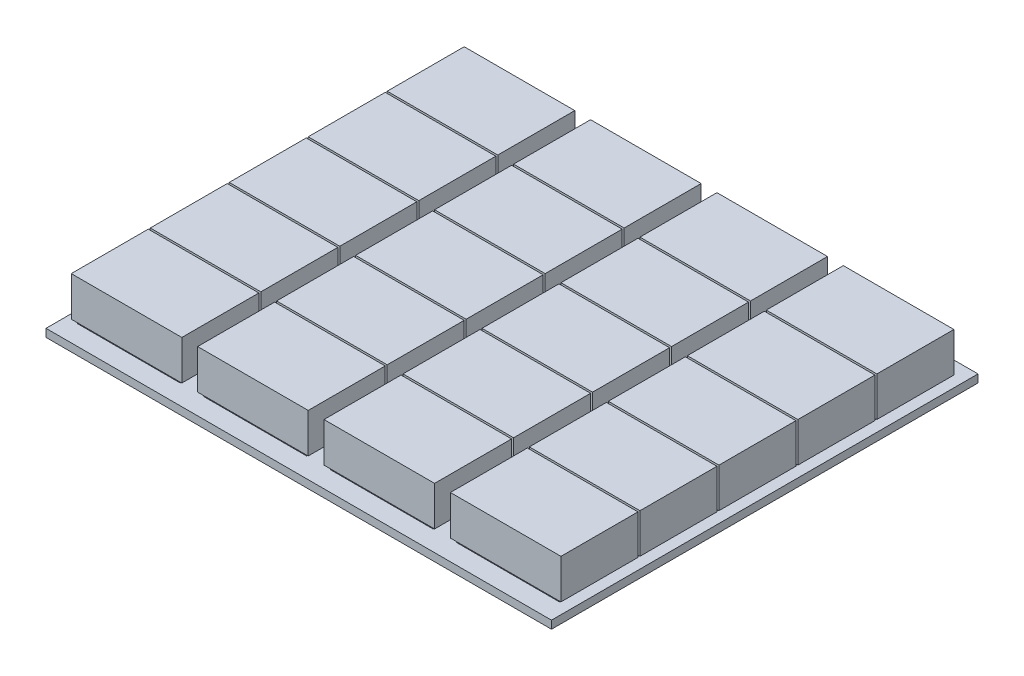
SolidWorks part; units mm, degrees
ref_plane "Front Plane" through (0, 0, 0) normal (0, 0, 1) x (1, 0, 0)
ref_plane "Top Plane" through (0, 0, 0) normal (0, 1, 0) x (1, 0, 0)
ref_plane "Right Plane" through (0, 0, 0) normal (1, 0, 0) x (0, 0, -1)
sketch "Sketch1" plane through (0, 0, 0) normal (0, 1, 0) x (1, 0, 0)
  line L1 (-40, -135) -> (40, -135)
  line L2 (-40, -135) -> (-40, 135)
  line L3 (-40, 135) -> (40, 135)
  line L4 (40, -135) -> (40, 135)
  line L5 (-40, -135) -> (40, 135) construction
  line L6 (-40, 135) -> (40, -135) construction
  point P0 (0, 0)
  dimension "D1" = 80
  dimension "D2" = 270
extrude "Boss-Extrude1" add sketch "Sketch1" along normal blind 5
sketch "Sketch2" plane through (0, 5, 0) normal (0, 1, 0) x (1, 0, 0)
  line L0 (0, 0) -> (0, -135) construction
  line L1 (-40, -135) -> (40, -135) construction
  line L3 (-32.5, -77.5) -> (32.5, -77.5)
  line L4 (-32.5, -77.5) -> (-32.5, -122.5)
  line L5 (-32.5, -122.5) -> (32.5, -122.5)
  line L6 (32.5, -77.5) -> (32.5, -122.5)
  line L7 (-32.5, -77.5) -> (32.5, -122.5) construction
  line L8 (-32.5, -122.5) -> (32.5, -77.5) construction
  point P5 (0, -100)
  dimension "D1" = 65
  dimension "D2" = 45
  dimension "D3" = 12.5
extrude "Boss-Extrude3" add sketch "Sketch2" along normal blind 2
pattern_linear "LPattern1" count 5 spacing 50 along (0, 0, -1) of "Boss-Extrude3"
sketch "Sketch3" plane through (0, 7, 0) normal (0, 1, 0) x (1, 0, 0)
  line L0 (0, 0) -> (0, -122.5) construction
  line L1 (-32.5, -122.5) -> (32.5, -122.5) construction
  line L2 (-40, 135) -> (-40, -135) construction
  line L3 (-35, -75.2605) -> (35, -75.2605)
  line L4 (-35, -75.2605) -> (-35, -124.0095)
  line L5 (-35, -124.0095) -> (35, -124.0095)
  line L6 (35, -75.2605) -> (35, -124.0095)
  line L7 (-35, -75.2605) -> (35, -124.0095) construction
  line L8 (-35, -124.0095) -> (35, -75.2605) construction
  point P5 (0, -99.635)
  dimension "D1" = 5
extrude "Boss-Extrude8" add sketch "Sketch3" along normal blind 25
pattern_linear "LPattern5" count 5 spacing 50 along (0, 0, -1) of "Boss-Extrude8"
pattern_linear "LPattern6" count 4 spacing 80 along (-1, 0, 0) of "Boss-Extrude1", "Boss-Extrude3", "LPattern1", "Boss-Extrude8", "LPattern5"
